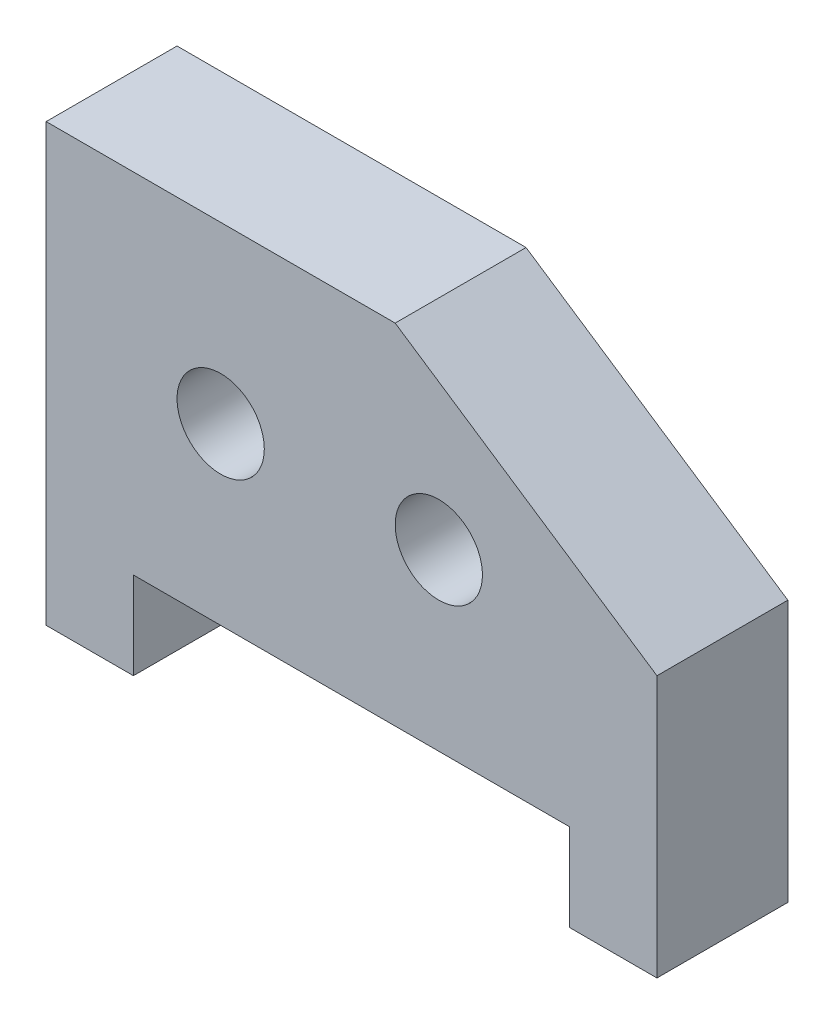
SolidWorks part; units mm, degrees
ref_plane "Front Plane" through (0, 0, 0) normal (0, 0, 1) x (1, 0, 0)
ref_plane "Top Plane" through (0, 0, 0) normal (0, 1, 0) x (1, 0, 0)
ref_plane "Right Plane" through (0, 0, 0) normal (1, 0, 0) x (0, 0, -1)
sketch "Sketch1" plane through (0, 0, 0) normal (0, 0, 1) x (1, 0, 0)
  line L0 (-1.3047, 61.9985) -> (-1.3047, -1.5015)
  line L1 (-1.3047, -1.5015) -> (11.3953, -1.5015)
  line L2 (11.3953, -1.5015) -> (11.3953, 11.1985)
  line L3 (11.3953, 11.1985) -> (74.8953, 11.1985)
  line L4 (74.8953, 11.1985) -> (74.8953, -1.5015)
  line L5 (74.8953, -1.5015) -> (87.5953, -1.5015)
  line L6 (87.5953, -1.5015) -> (87.5953, 36.5985)
  line L7 (87.5953, 36.5985) -> (49.4953, 61.9985)
  line L8 (49.4953, 61.9985) -> (-1.3047, 61.9985)
  circle A0 centre (24.0953, 36.5985) radius 6.35
  circle A1 centre (55.8453, 36.5985) radius 6.35
  dimension "D8" = 12.7
  dimension "D10" = 25.4
  dimension "D11" = 25.4
  dimension "D1" = 88.9
  dimension "D2" = 12.7
  dimension "D3" = 2
  dimension "D4" = 63.5
  dimension "D5" = 12.7
  dimension "D6" = 38.1
  dimension "D7" = 50.8
  dimension "D9" = 63.5
extrude "Boss-Extrude1" add sketch "Sketch1" along normal blind 19.05
equation "\"in\"=0.75"
